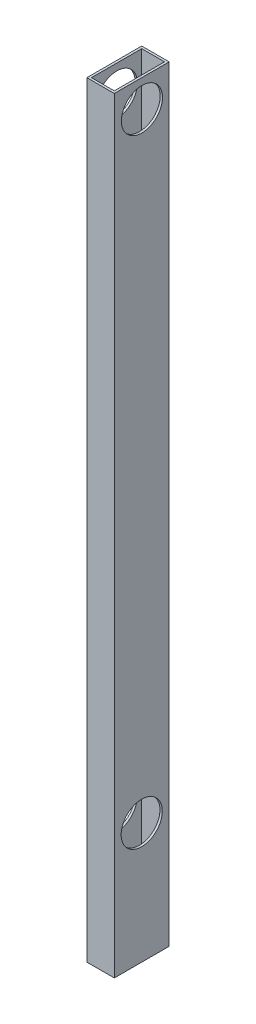
SolidWorks part; units mm, degrees
ref_plane "Front Plane" through (0, 0, 0) normal (0, 0, 1) x (1, 0, 0)
ref_plane "Top Plane" through (0, 0, 0) normal (0, 1, 0) x (1, 0, 0)
ref_plane "Right Plane" through (0, 0, 0) normal (1, 0, 0) x (0, 0, -1)
sketch "Sketch1" plane through (0, 0, 0) normal (0, 1, 0) x (1, 0, 0)
  line L1 (0, 0) -> (19.05, 0)
  line L2 (0, 0) -> (0, 38.1)
  line L3 (0, 38.1) -> (19.05, 38.1)
  line L4 (19.05, 0) -> (19.05, 38.1)
  dimension "D1" = 38.1
  dimension "D2" = 19.05
extrude "Extrude-Thin1" add sketch "Sketch1" along normal blind 457.2 thin thin type one direction reverse wall 1.5875
sketch "Sketch3" plane through (0, 0, 0) normal (0, -1, 0) x (-1, 0, 0)
  line L1 (-19.05, 38.1) -> (0, 38.1)
  line L2 (-19.05, 38.1) -> (-19.05, 0)
  line L3 (-19.05, 0) -> (0, 0)
  line L4 (0, 38.1) -> (0, 0)
extrude "Extrude-Thin2" add sketch "Sketch3" along normal blind 75.184 thin
sketch "Sketch4" plane through (19.05, 0, 0) normal (1, 0, 0) x (0, 0, -1)
  line L0 (0, 457.2) -> (38.1, 457.2) construction
  line L1 (0, 457.2) -> (0, -75.184) construction
  line L2 (38.1, -75.184) -> (0, -75.184) construction
  circle A0 centre (19.2024, 438.15) radius 14.2875
  circle A1 centre (19.05, 8.636) radius 14.2875
  point P6 (0, 0)
  dimension "D1" = 28.575
  dimension "D2" = 28.575
  dimension "D4" = 19.2024
  dimension "D5" = 83.82
  dimension "D3" = 19.05
  dimension "D6" = 19.05
extrude "Cut-Extrude1" cut sketch "Sketch4" against normal through all
